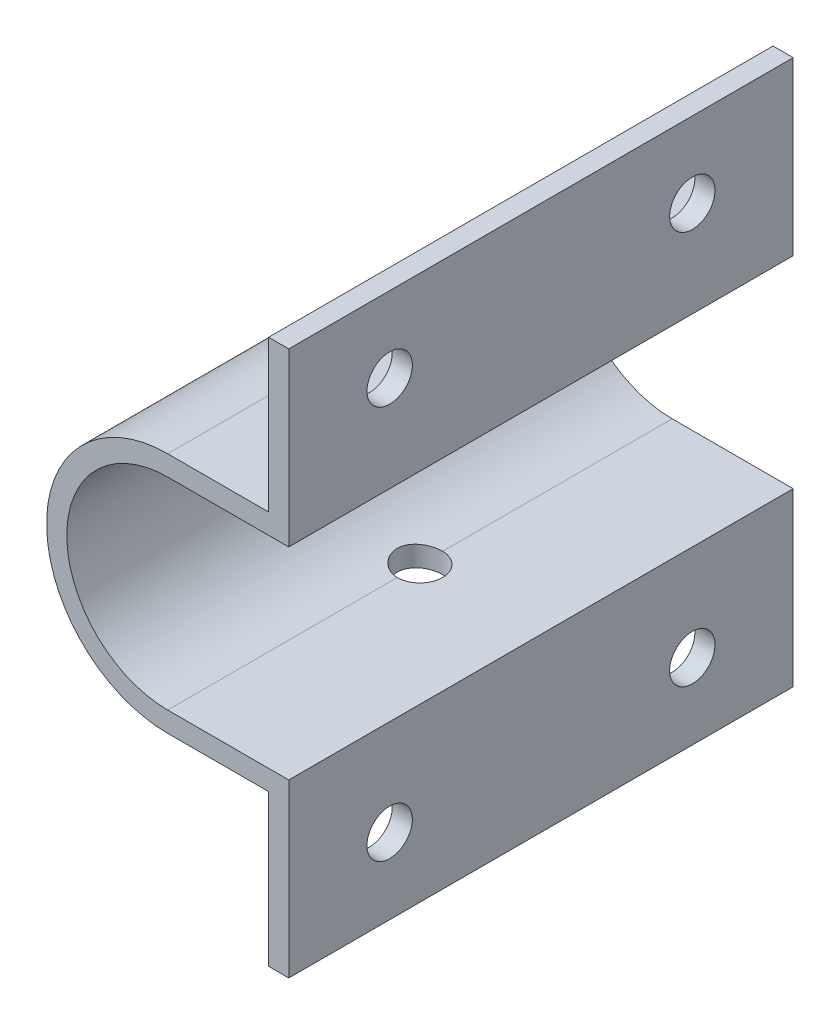
SolidWorks part; units mm, degrees
ref_plane "Front Plane" through (0, 0, 0) normal (0, 0, 1) x (1, 0, 0)
ref_plane "Top Plane" through (0, 0, 0) normal (0, 1, 0) x (1, 0, 0)
ref_plane "Right Plane" through (0, 0, 0) normal (1, 0, 0) x (0, 0, -1)
sketch "Sketch1" plane through (0, 0, 0) normal (0, 0, 1) x (1, 0, 0)
  line L2 (0, 10) -> (0, -10) construction
  line L3 (0, 12) -> (10, 12)
  line L5 (12, 10) -> (0, 10)
  line L6 (0, -10) -> (12, -10)
  line L8 (10, -12) -> (0, -12)
  line L9 (10, 12) -> (10, 27)
  line L10 (10, 27) -> (12, 27)
  line L11 (12, 27) -> (12, 10)
  line L14 (12, -10) -> (12, -27)
  line L15 (12, -27) -> (10, -27)
  line L16 (10, -27) -> (10, -12)
  arc A0 (0, 10) -> (0, -10) centre (0, 0) ccw
  arc A1 (0, 12) -> (0, -12) centre (0, 0) ccw
  dimension "D1" = 10
  dimension "D2" = 2
  dimension "D3" = 10
  dimension "D4" = 15
  dimension "D5" = 2
extrude "Boss-Extrude1" add sketch "Sketch1" along normal blind 50
sketch "Sketch2" plane through (0, 12, 0) normal (0, 1, 0) x (1, 0, 0)
  line L0 (0, -50) -> (0, 0) construction
  circle A0 centre (0, -25) radius 2.25
  dimension "D1" = 4.5
extrude "Cut-Extrude1" cut sketch "Sketch2" against normal up to surface (24 mm away) up to face at (5, -12, 25)
sketch "Sketch3" plane through (10, 0, 0) normal (-1, 0, 0) x (0, 0, 1)
  line L0 (0, 19.5) -> (12.25, 19.5) construction
  line L1 (0, 27) -> (0, 12) construction
  line L2 (50, 27) -> (50, 12) construction
  line L3 (50, -19.5) -> (37.75, -19.5) construction
  line L4 (50, -12) -> (50, -27) construction
  line L5 (0, -12) -> (0, -27) construction
  line L6 (37.75, 19.5) -> (50, 19.5) construction
  line L7 (12.25, -19.5) -> (0, -19.5) construction
  circle A0 centre (10, 19.5) radius 2.25
  circle A1 centre (40, 19.5) radius 2.25
  circle A2 centre (40, -19.5) radius 2.25
  circle A3 centre (10, -19.5) radius 2.25
  dimension "D1" = 4.5
  dimension "D2" = 10
extrude "Cut-Extrude2" cut sketch "Sketch3" against normal up to next
